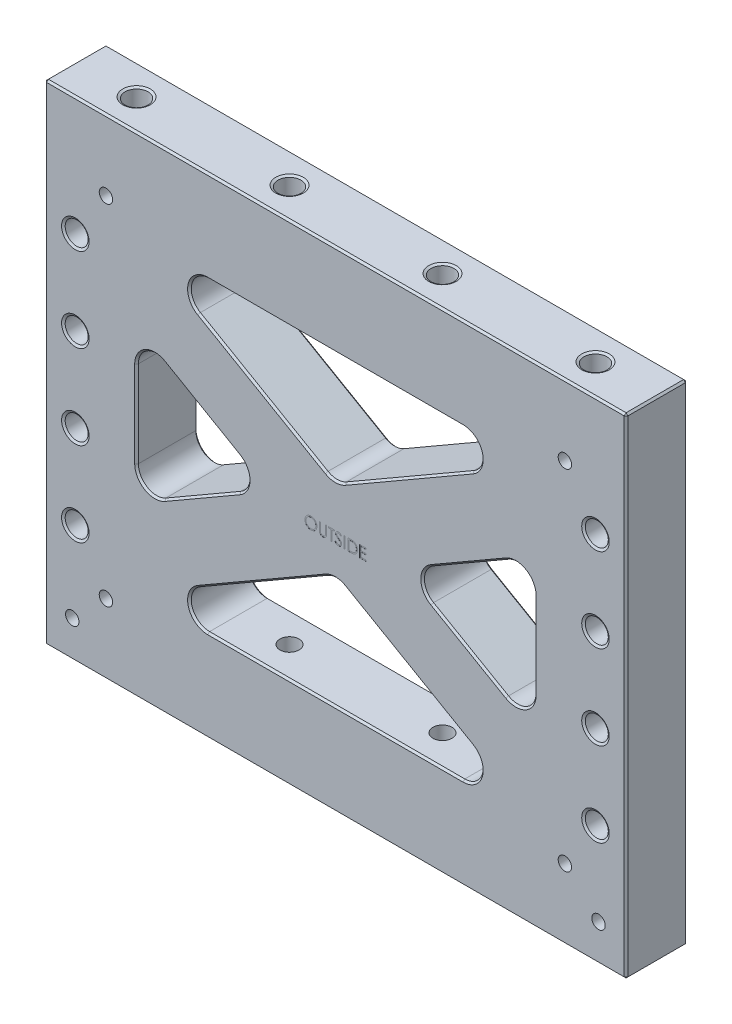
SolidWorks part; units mm, degrees
material "6061-T6 Al"
ref_plane "Front" through (0, 0, 0) normal (0, 0, 1) x (1, 0, 0)
ref_plane "Top" through (0, 0, 0) normal (0, 1, 0) x (1, 0, 0)
ref_plane "Right" through (0, 0, 0) normal (1, 0, 0) x (0, 0, -1)
sketch "Sketch1" plane through (0, 0, 0) normal (0, 0, 1) x (1, 0, 0)
  line L1 (-120.65, 0) -> (120.65, 0)
  line L2 (-120.65, 0) -> (-120.65, 203.2)
  line L3 (-120.65, 203.2) -> (120.65, 203.2)
  line L4 (120.65, 0) -> (120.65, 203.2)
  dimension "D1" = 241.3
  dimension "D2" = 203.2
extrude "Extrude1" add sketch "Sketch1" along normal blind 25.4
sketch "Sketch2" plane through (0, 0, 25.4) normal (0, 0, 1) x (1, 0, 0)
  line L0 (0, 165.1) -> (0, 203.2) construction
  line L1 (-82.55, 165.1) -> (82.55, 165.1)
  line L2 (-82.55, 165.1) -> (-82.55, 38.1)
  line L3 (-82.55, 38.1) -> (82.55, 38.1)
  line L4 (82.55, 165.1) -> (82.55, 38.1)
  line L5 (120.65, 203.2) -> (-120.65, 203.2) construction
  line L6 (0, 0) -> (0, 38.1) construction
  line L7 (120.65, 0) -> (120.65, 203.2) construction
  dimension "D1" = 38.1
  dimension "D2" = 38.1
extrude "Extrude2" cut sketch "Sketch2" against normal through all
sketch "Sketch3" plane through (0, 0, 25.4) normal (0, 0, 1) x (1, 0, 0)
  line L0 (81.4102, 38.1) -> (-138.5602, 165.1) construction
  line L1 (-82.55, 38.1) -> (82.55, 38.1) construction
  line L2 (-82.55, 149.2603) -> (82.55, 53.9397) construction
  line L3 (-82.55, 165.1) -> (-82.55, 38.1) construction
  line L4 (-82.55, 132.7625) -> (-82.55, 165.1)
  line L5 (-82.55, 165.1) -> (-81.4102, 165.1)
  line L6 (-81.4102, 165.1) -> (138.5602, 38.1) construction
  line L7 (-81.4102, 165.1) -> (82.55, 70.4375)
  line L8 (82.55, 38.1) -> (82.55, 165.1) construction
  line L9 (82.55, 70.4375) -> (82.55, 38.1)
  line L10 (82.55, 38.1) -> (81.4102, 38.1)
  line L11 (0, 101.6) -> (120.65, 101.6) construction
  line L12 (120.65, 0) -> (120.65, 203.2) construction
  line L13 (0, 101.6) -> (-7.1437, 89.2267) construction
  line L14 (0, 101.6) -> (7.1437, 113.9733) construction
  line L15 (82.55, 165.1) -> (-82.55, 165.1) construction
  line L16 (-81.4102, 165.1) -> (-138.5602, 165.1) construction
  line L17 (81.4102, 38.1) -> (-82.55, 132.7625)
  line L18 (81.4102, 38.1) -> (138.5602, 38.1) construction
  point P1 (0, 101.6)
  dimension "D1" = 30
  dimension "D2" = 28.575
extrude "Extrude3" add sketch "Sketch3" against normal up to surface (25.4 mm away) up to face at (0, 101.6, 0)
mirror "Mirror1" about plane through (0, 0, 0) normal (1, 0, 0) of "Extrude3"
fillet "Fillet1" radius 7.62 12 edges at (-81.4102, 38.1, 12.7) (81.4102, 38.1, 12.7) (0, 85.1022, 12.7) (81.4102, 165.1, 12.7) (-82.55, 132.7625, 12.7) (-82.55, 70.4375, 12.7) (-28.575, 101.6, 12.7) (82.55, 70.4375, 12.7) (82.55, 132.7625, 12.7) (28.575, 101.6, 12.7) (0, 118.0978, 12.7) (-81.4102, 165.1, 12.7)
chamfer "Chamfer1" distance 0.762 angle 45 48 edges at (30.296, 67.6108, 25.4) (30.296, 67.6108, 0) (60.3324, 43.7478, 0) (60.3324, 43.7478, 25.4) (0, 83.9234, 25.4) (0, 83.9234, 0) (0, 38.1, 0) (0, 38.1, 25.4) (-30.296, 67.6108, 25.4) (-60.3324, 43.7478, 0) (-60.3324, 43.7478, 25.4) (-30.296, 67.6108, 0) (82.55, 101.6, 0) (82.55, 101.6, 25.4) (78.74, 77.0366, 0) (78.74, 77.0366, 25.4) (78.74, 126.1634, 0) (78.74, 126.1634, 25.4) (55.5625, 86.0188, 25.4) (55.5625, 86.0188, 0) (55.5625, 117.1812, 25.4) (36.195, 101.6, 0) (36.195, 101.6, 25.4) (55.5625, 117.1812, 0) (30.296, 135.5892, 25.4) (0, 119.2766, 25.4) (0, 119.2766, 0) (60.3324, 159.4522, 0) (60.3324, 159.4522, 25.4) (-30.296, 135.5892, 25.4) (-30.296, 135.5892, 0) (0, 165.1, 0) (0, 165.1, 25.4) (-60.3324, 159.4522, 0) (-60.3324, 159.4522, 25.4) (30.296, 135.5892, 0) (-36.195, 101.6, 0) (-36.195, 101.6, 25.4) (-55.5625, 117.1812, 25.4) (-55.5625, 117.1812, 0) (-55.5625, 86.0188, 25.4) (-78.74, 126.1634, 0) (-78.74, 126.1634, 25.4) (-78.74, 77.0366, 0) (-78.74, 77.0366, 25.4) (-82.55, 101.6, 0) (-82.55, 101.6, 25.4) (-55.5625, 86.0188, 0)
chamfer "Chamfer2" distance 0.762 angle 45 12 edges at (0, 0, 0) (0, 0, 25.4) (-120.65, 101.6, 0) (-120.65, 101.6, 25.4) (-120.65, 0, 12.7) (0, 203.2, 0) (0, 203.2, 25.4) (-120.65, 203.2, 12.7) (120.65, 0, 12.7) (120.65, 101.6, 0) (120.65, 101.6, 25.4) (120.65, 203.2, 12.7)
hole_wizard "3/8-16 Tapped Hole1" positions "Sketch7" profile "Sketch6" tap size "3/8-16" standard "Ansi Inch"
sketch "Sketch7" plane through (0, 203.2, 0) normal (0, 1, 0) x (-1, 0, 0)
  line L1 (-95.25, 12.7) -> (-31.75, 12.7) construction
  line L2 (-31.75, 12.7) -> (31.75, 12.7) construction
  line L3 (31.75, 12.7) -> (95.25, 12.7) construction
  line L6 (120.65, 25.4) -> (120.65, 0) construction
  point P1 (31.75, 12.7)
  point P3 (-31.75, 12.7)
  point P25 (0, 12.7)
  point P29 (120.65, 12.7)
  dimension "D1" = 63.5
sketch "Sketch6" plane through (-31.75, 203.2, 12.7) normal (1, 0, 0) x (0, 0, 1)
  line L0 (0, 0) -> (0, 40.4847)
  line L1 (0, 40.4847) -> (3.9687, 38.1)
  line L2 (3.9687, 38.1) -> (3.9687, 25.4)
  line L3 (3.9687, 25.4) -> (4.7625, 25.4)
  line L5 (4.7625, 25.4) -> (4.7625, 0.5499)
  line L6 (4.7625, 0.5499) -> (5.715, 0)
  line L7 (5.715, 0) -> (0, 0)
  line L8 (-4.7625, 0.5499) -> (-5.715, 0) construction
  line L10 (0, 40.4847) -> (-3.9688, 38.1) construction
  line L11 (0, -6.35) -> (0, 107.95) construction
  dimension "Tap Drill Dia." = 7.9375
  dimension "Tap Drill Depth" = 38.1
  dimension "Thread Major Dia." = 9.525
  dimension "Thread Depth" = 25.4
  dimension "Near C'Sink Dia." = 11.43
  dimension "Near C'Sink Angle" = 120
  dimension "Drill Angle" = 118
hole_wizard "3/8-16 Tapped Hole2" positions "Sketch9" profile "Sketch8" tap size "3/8-16" standard "Ansi Inch"
sketch "Sketch9" plane through (0, 0, 0) normal (0, -1, 0) x (1, 0, 0)
  point P1 (-31.75, 12.7)
  point P4 (31.75, 12.7)
sketch "Sketch8" plane through (-31.75, 0, 12.7) normal (1, 0, 0) x (0, 0, -1)
  line L0 (0, 0) -> (0, 40.4847)
  line L1 (0, 40.4847) -> (3.9687, 38.1)
  line L2 (3.9687, 38.1) -> (3.9687, 25.4)
  line L3 (3.9687, 25.4) -> (4.7625, 25.4)
  line L5 (4.7625, 25.4) -> (4.7625, 0.5499)
  line L6 (4.7625, 0.5499) -> (5.715, 0)
  line L7 (5.715, 0) -> (0, 0)
  line L8 (-4.7625, 0.5499) -> (-5.715, 0) construction
  line L10 (0, 40.4847) -> (-3.9688, 38.1) construction
  line L11 (0, -6.35) -> (0, 107.95) construction
  dimension "Tap Drill Dia." = 7.9375
  dimension "Tap Drill Depth" = 38.1
  dimension "Thread Major Dia." = 9.525
  dimension "Thread Depth" = 25.4
  dimension "Near C'Sink Dia." = 11.43
  dimension "Near C'Sink Angle" = 120
  dimension "Drill Angle" = 118
hole_wizard "3/8-16 Tapped Hole3" positions "Sketch11" profile "Sketch10" tap size "3/8-16" standard "Ansi Inch"
sketch "Sketch11" plane through (0, 203.2, 0) normal (0, 1, 0) x (-1, 0, 0)
  line L0 (-95.25, 12.7) -> (-31.75, 12.7) construction
  line L1 (-31.75, 12.7) -> (31.75, 12.7) construction
  line L2 (31.75, 12.7) -> (95.25, 12.7) construction
  point P0 (95.25, 12.7)
  point P2 (-95.25, 12.7)
sketch "Sketch10" plane through (-95.25, 203.2, 12.7) normal (1, 0, 0) x (0, 0, 1)
  line L0 (0, 0) -> (0, 40.4847)
  line L1 (0, 40.4847) -> (3.9687, 38.1)
  line L2 (3.9687, 38.1) -> (3.9687, 25.4)
  line L3 (3.9687, 25.4) -> (4.7625, 25.4)
  line L5 (4.7625, 25.4) -> (4.7625, 0.5499)
  line L6 (4.7625, 0.5499) -> (5.715, 0)
  line L7 (5.715, 0) -> (0, 0)
  line L8 (-4.7625, 0.5499) -> (-5.715, 0) construction
  line L10 (0, 40.4847) -> (-3.9688, 38.1) construction
  line L11 (0, -6.35) -> (0, 107.95) construction
  dimension "Tap Drill Dia." = 7.9375
  dimension "Tap Drill Depth" = 38.1
  dimension "Thread Major Dia." = 9.525
  dimension "Thread Depth" = 25.4
  dimension "Near C'Sink Dia." = 11.43
  dimension "Near C'Sink Angle" = 120
  dimension "Drill Angle" = 118
hole_wizard "3/8-16 Tapped Hole4" positions "Sketch13" profile "Sketch12" tap size "3/8-16" standard "Ansi Inch"
sketch "Sketch13" plane through (0, 0, 0) normal (0, -1, 0) x (1, 0, 0)
  point P0 (-95.25, 12.7)
  point P1 (95.25, 12.7)
sketch "Sketch12" plane through (-95.25, 0, 12.7) normal (1, 0, 0) x (0, 0, -1)
  line L0 (0, 0) -> (0, 40.4847)
  line L1 (0, 40.4847) -> (3.9687, 38.1)
  line L2 (3.9687, 38.1) -> (3.9687, 25.4)
  line L3 (3.9687, 25.4) -> (4.7625, 25.4)
  line L5 (4.7625, 25.4) -> (4.7625, 0.5499)
  line L6 (4.7625, 0.5499) -> (5.715, 0)
  line L7 (5.715, 0) -> (0, 0)
  line L8 (-4.7625, 0.5499) -> (-5.715, 0) construction
  line L10 (0, 40.4847) -> (-3.9688, 38.1) construction
  line L11 (0, -6.35) -> (0, 107.95) construction
  dimension "Tap Drill Dia." = 7.9375
  dimension "Tap Drill Depth" = 38.1
  dimension "Thread Major Dia." = 9.525
  dimension "Thread Depth" = 25.4
  dimension "Near C'Sink Dia." = 11.43
  dimension "Near C'Sink Angle" = 120
  dimension "Drill Angle" = 118
hole_wizard "7/32 (0.21875) Vent Hole1" positions "Sketch5" profile "Sketch4" hole size "7/32" standard "Ansi Inch" end condition through all
sketch "Sketch5" plane through (0, 0, 25.4) normal (0, 0, 1) x (1, 0, 0)
  line L0 (-95.25, 173.99) -> (-31.75, 173.99) construction
  line L1 (-31.75, 173.99) -> (31.75, 173.99) construction
  line L2 (31.75, 173.99) -> (95.25, 173.99) construction
  line L5 (0, -13.97) -> (0, 13.97) construction
  line L6 (120.65, 203.2) -> (-120.65, 203.2) construction
  line L7 (-95.25, 173.99) -> (-95.25, 203.2) construction
  line L10 (-95.25, 29.21) -> (-95.25, 0) construction
  line L11 (-120.65, 0) -> (120.65, 0) construction
  line L13 (-119.888, 203.2) -> (119.888, 203.2) construction
  point P0 (-95.25, 173.99)
  point P5 (95.25, 173.99)
  point P7 (-95.25, 29.21)
  point P13 (95.25, 29.21)
  point P26 (0, 173.99)
  dimension "D1" = 63.5
  dimension "D2" = 29.21
sketch "Sketch4" plane through (-95.25, 173.99, 25.4) normal (1, 0, 0) x (0, -1, 0)
  line L0 (0, 0) -> (0, 25.4)
  line L1 (0, 25.4) -> (2.7781, 25.4)
  line L2 (2.7781, 25.4) -> (2.7781, 0)
  line L5 (2.7781, 0) -> (0, 0)
  line L11 (0, -6.35) -> (0, 107.95) construction
  dimension "Thru Hole Dia." = 5.5562
  dimension "Thru Hole Depth" = 25.4
hole_wizard "3/8-16 Tapped Hole5" positions "Sketch15" profile "Sketch14" tap size "3/8-16" standard "Ansi Inch" end condition through all
sketch "Sketch15" plane through (8.7974, 80.9292, 0) normal (0, 0, 1) x (1, 0, 0)
  line L0 (99.1526, 73.0583) -> (111.8526, 73.0583) construction
  line L1 (111.8526, 121.5088) -> (111.8526, -80.1672) construction
  line L6 (-116.7474, 73.0583) -> (-116.7474, 38.1333) construction
  line L7 (-116.7474, 38.1333) -> (-116.7474, 3.2083) construction
  line L8 (-116.7474, 3.2083) -> (-116.7474, -31.7167) construction
  line L11 (-116.7474, 20.6708) -> (-129.4474, 20.6708) construction
  line L12 (-129.4474, -80.1672) -> (-129.4474, 121.5088) construction
  point P0 (-116.7474, 73.0583)
  point P1 (-116.7474, 38.1333)
  point P3 (-116.7474, 3.2083)
  point P5 (-116.7474, -31.7167)
  point P7 (99.1526, 73.0583)
  point P9 (99.1526, 38.1333)
  point P11 (99.1526, 3.2083)
  point P13 (99.1526, -31.7167)
  dimension "D1" = 12.7
  dimension "D2" = 34.925
sketch "Sketch14" plane through (-107.95, 153.9875, 0) normal (1, 0, 0) x (0, 1, 0)
  line L0 (0, 0) -> (0, 25.4)
  line L1 (0, 25.4) -> (5.715, 25.4)
  line L2 (4.7625, 24.8501) -> (4.7625, 0.5499)
  line L3 (4.7625, 0.5499) -> (5.715, 0)
  line L5 (5.715, 0) -> (0, 0)
  line L6 (-4.7625, 0.5499) -> (-5.715, 0) construction
  line L7 (5.715, 25.4) -> (4.7625, 24.8501)
  line L8 (-5.715, 25.4) -> (-4.7625, 24.8501) construction
  line L11 (0, -6.35) -> (0, 107.95) construction
  dimension "Thread Major Dia." = 9.525
  dimension "Thru Tap Drill Depth" = 25.4
  dimension "Near C'Sink Dia." = 11.43
  dimension "Near C'Sink Angle" = 120
  dimension "Far C'Sink Dia." = 11.43
  dimension "Far C'Sink Angle" = 120
sketch "Sketch16" [suppressed] plane through (0, 0, 0) normal (0, -1, 0) x (1, 0, 0)
  line L4 (-120.65, 0) -> (120.65, 0)
  line L5 (120.65, 0) -> (120.65, 25.4)
  line L6 (120.65, 25.4) -> (-120.65, 25.4)
  line L7 (-120.65, 25.4) -> (-120.65, 0)
  line L8 (-120.65, 0) -> (120.65, 0)
  line L9 (120.65, 0) -> (120.65, 25.4)
  line L10 (120.65, 25.4) -> (-120.65, 25.4)
  line L11 (-120.65, 25.4) -> (-120.65, 0)
  dimension "D1" = 0
extrude "Extrude4" [suppressed] cut sketch "Sketch16" against normal blind 0.0254
sketch "Sketch17" [suppressed] plane through (0, 0.0254, 0) normal (0, -1, 0) x (1, 0, 0)
  line L0 (120.65, 25.4) -> (-120.65, 25.4) construction
  line L1 (-44.45, 25.4) -> (-19.05, 25.4)
  line L2 (-44.45, 25.4) -> (-44.45, 0)
  line L3 (-44.45, 0) -> (-19.05, 0)
  line L4 (-19.05, 25.4) -> (-19.05, 0)
  line L5 (-120.65, 0) -> (120.65, 0) construction
  line L6 (-19.05, 12.7) -> (19.05, 12.7) construction
  line L7 (-107.95, 25.4) -> (-82.55, 25.4)
  line L8 (-107.95, 25.4) -> (-107.95, 0)
  line L9 (-107.95, 0) -> (-82.55, 0)
  line L10 (-82.55, 25.4) -> (-82.55, 0)
  line L11 (19.05, 25.4) -> (44.45, 25.4)
  line L12 (19.05, 25.4) -> (19.05, 0)
  line L13 (19.05, 0) -> (44.45, 0)
  line L14 (44.45, 25.4) -> (44.45, 0)
  line L15 (82.55, 25.4) -> (107.95, 25.4)
  line L16 (82.55, 25.4) -> (82.55, 0)
  line L17 (82.55, 0) -> (107.95, 0)
  line L18 (107.95, 25.4) -> (107.95, 0)
  line L19 (44.45, 12.7) -> (82.55, 12.7) construction
  line L20 (-82.55, 12.7) -> (-44.45, 12.7) construction
  point P26 (0, 12.7)
  dimension "D1" = 25.4
  dimension "D2" = 38.1
extrude "Extrude5" [suppressed] add sketch "Sketch17" along normal blind 0.0254
sketch "Sketch19" [suppressed] plane through (0, 184.15, 0) normal (0, 1, 0) x (1, 0, 0)
  line L4 (120.65, 0) -> (-120.65, 0)
  line L5 (-120.65, 0) -> (-120.65, -25.4)
  line L6 (-120.65, -25.4) -> (120.65, -25.4)
  line L7 (120.65, -25.4) -> (120.65, 0)
  line L8 (120.65, 0) -> (-120.65, 0)
  line L9 (-120.65, 0) -> (-120.65, -25.4)
  line L10 (-120.65, -25.4) -> (120.65, -25.4)
  line L11 (120.65, -25.4) -> (120.65, 0)
  dimension "D1" = 0
extrude "Extrude7" [suppressed] cut sketch "Sketch19" against normal blind 0.0254
sketch "Sketch18" [suppressed] plane through (0, 184.1246, 0) normal (0, 1, 0) x (1, 0, 0)
  line L1 (-44.45, 0) -> (-19.05, 0)
  line L2 (-44.45, 0) -> (-44.45, -25.4)
  line L3 (-44.45, -25.4) -> (-19.05, -25.4)
  line L4 (-19.05, 0) -> (-19.05, -25.4)
  line L6 (-82.55, -12.7) -> (-44.45, -12.7) construction
  line L7 (-107.95, 0) -> (-82.55, 0)
  line L8 (-107.95, 0) -> (-107.95, -25.4)
  line L9 (-107.95, -25.4) -> (-82.55, -25.4)
  line L10 (-82.55, 0) -> (-82.55, -25.4)
  line L11 (19.05, 0) -> (44.45, 0)
  line L12 (19.05, 0) -> (19.05, -25.4)
  line L13 (19.05, -25.4) -> (44.45, -25.4)
  line L14 (44.45, 0) -> (44.45, -25.4)
  line L15 (82.55, 0) -> (107.95, 0)
  line L16 (82.55, 0) -> (82.55, -25.4)
  line L17 (82.55, -25.4) -> (107.95, -25.4)
  line L18 (107.95, 0) -> (107.95, -25.4)
  line L19 (-19.05, -12.7) -> (19.05, -12.7) construction
  line L20 (44.45, -12.7) -> (82.55, -12.7) construction
  line L21 (120.65, 0) -> (-120.65, 0) construction
  line L22 (-120.65, -25.4) -> (120.65, -25.4) construction
  point P26 (0, -12.7)
  dimension "D1" = 38.1
  dimension "D2" = 25.4
extrude "Extrude6" [suppressed] add sketch "Sketch18" along normal blind 0.0254
sketch "Sketch20" [suppressed] plane through (0, 184.15, 0) normal (0, 1, 0) x (1, 0, 0)
  line L0 (107.95, -25.4) -> (107.95, 0) construction
  line L1 (-107.95, 0) -> (107.95, 0)
  line L2 (-107.95, 0) -> (-107.95, -3.81)
  line L3 (-107.95, -3.81) -> (107.95, -3.81)
  line L4 (107.95, 0) -> (107.95, -3.81)
  line L5 (107.95, -25.4) -> (120.65, -25.4) construction
  line L6 (107.95, -25.4) -> (-107.95, -25.4)
  line L7 (107.95, -25.4) -> (107.95, -21.59)
  line L8 (107.95, -21.59) -> (-107.95, -21.59)
  line L9 (-107.95, -25.4) -> (-107.95, -21.59)
  line L10 (-107.95, 0) -> (-107.95, -25.4) construction
  dimension "D1" = 3.81
extrude "Extrude8" [suppressed] cut sketch "Sketch20" against normal up to surface (0.0254 mm away)
sketch "Sketch21" [suppressed] plane through (0, 0, 0) normal (0, -1, 0) x (1, 0, 0)
  line L0 (107.95, 0) -> (107.95, 25.4) construction
  line L1 (-107.95, 25.4) -> (107.95, 25.4)
  line L2 (-107.95, 25.4) -> (-107.95, 21.59)
  line L3 (-107.95, 21.59) -> (107.95, 21.59)
  line L4 (107.95, 25.4) -> (107.95, 21.59)
  line L6 (-107.95, 0) -> (107.95, 0)
  line L7 (-107.95, 0) -> (-107.95, 3.81)
  line L8 (-107.95, 3.81) -> (107.95, 3.81)
  line L9 (107.95, 0) -> (107.95, 3.81)
  dimension "D1" = 3.81
extrude "Extrude9" [suppressed] cut sketch "Sketch21" against normal up to surface (0.0254 mm away)
sketch "Sketch22" [suppressed] plane through (0, 0, 25.4) normal (0, 0, 1) x (1, 0, 0)
  line L0 (-82.55, 125.0706) -> (-82.55, 59.0794)
  line L1 (-82.55, 59.0794) -> (-25.4, 92.075)
  line L2 (-25.4, 92.075) -> (-82.55, 125.0706)
  line L3 (0, 0) -> (0, 139.6976) construction
  line L4 (33.02, 92.075) -> (104.387, 92.075) construction
  line L5 (-71.12, 65.6785) -> (-36.83, 85.4759) construction
  line L6 (-82.55, 111.8723) -> (-82.55, 72.2777) construction
  line L7 (-71.12, 118.4715) -> (-36.83, 98.6741) construction
  line L8 (25.4, 92.075) -> (82.55, 125.0706)
  line L9 (82.55, 59.0794) -> (25.4, 92.075)
  line L10 (82.55, 125.0706) -> (82.55, 59.0794)
  line L11 (-68.0874, 146.05) -> (0, 106.7397)
  line L12 (0, 106.7397) -> (68.0874, 146.05)
  line L13 (68.0874, 146.05) -> (-68.0874, 146.05)
  line L14 (39.6492, 146.05) -> (-39.6492, 146.05) construction
  line L15 (3.81, 108.9394) -> (43.4592, 131.8309) construction
  line L16 (-3.81, 108.9394) -> (-43.4592, 131.8309) construction
  line L17 (0, 77.4103) -> (68.0874, 38.1)
  line L18 (68.0874, 38.1) -> (-68.0874, 38.1)
  line L19 (-68.0874, 38.1) -> (0, 77.4103)
  arc A0 (36.83, 98.6741) -> (36.83, 85.4759) centre (40.64, 92.075) ccw construction
extrude "Extrude10" [suppressed] cut sketch "Sketch22" against normal through all
hole_wizard "3/8 (0.375) Diameter Hole2" positions "Sketch32" profile "Sketch31" hole size "3/8" standard "Ansi Inch"
sketch "Sketch32" plane through (0, 0, 0) normal (0, -1, 0) x (1, 0, 0)
  line L0 (-109.22, 12.7) -> (109.22, 12.7) construction
  line L3 (-120.65, 0.762) -> (-120.65, 24.638) construction
  point P0 (-109.22, 12.7)
  point P7 (0, 12.7)
  point P11 (-120.65, 12.7)
  dimension "D1" = 13.97
sketch "Sketch31" plane through (-109.22, 0, 12.7) normal (1, 0, 0) x (0, 0, -1)
  line L0 (0, 0) -> (0, 21.9169)
  line L1 (0, 21.9169) -> (4.7714, 19.05)
  line L2 (4.7714, 19.05) -> (4.7714, 2.3406)
  line L3 (4.7714, 2.3406) -> (7.112, 0)
  line L5 (7.112, 0) -> (0, 0)
  line L6 (-4.7714, 2.3406) -> (-7.112, 0) construction
  line L10 (0, 21.9169) -> (-4.7714, 19.05) construction
  line L11 (0, -6.35) -> (0, 107.95) construction
  dimension "Hole Dia." = 9.5428
  dimension "Hole Depth" = 19.05
  dimension "Near C'Sink Dia." = 14.224
  dimension "Near C'Sink Angle" = 90
  dimension "Drill Angle" = 118
sketch "Sketch33" plane through (0, 0, 0) normal (0, -1, 0) x (1, 0, 0)
  line L0 (108.458, 12.7) -> (109.982, 12.7) construction
  line L1 (108.458, 17.4714) -> (109.982, 17.4714)
  line L2 (108.458, 7.9286) -> (109.982, 7.9286)
  arc A0 (108.458, 17.4714) -> (108.458, 7.9286) centre (108.458, 12.7) ccw
  arc A1 (109.982, 7.9286) -> (109.982, 17.4714) centre (109.982, 12.7) ccw
  circle A2 centre (-109.22, 12.7) radius 4.7714 construction
  point P2 (109.22, 12.7)
  dimension "D1" = 1.524
extrude "Extrude14" cut sketch "Sketch33" against normal blind 19.05
chamfer "Chamfer4" distance 2.286 angle 45 4 edges at (114.7534, 0, 12.7) (109.22, 0, 17.4714) (109.22, 0, 7.9286) (103.6866, 0, 12.7)
hole_wizard "7/32 (0.21875) Diameter Hole3" positions "Sketch35" profile "Sketch34" hole size "7/32" standard "Ansi Inch" end condition through all
sketch "Sketch35" plane through (0, 0, 25.4) normal (0, 0, 1) x (1, 0, 0)
  line L1 (-109.22, 15.24) -> (109.22, 15.24) construction
  line L2 (119.888, 0) -> (-119.888, 0) construction
  line L4 (-120.65, 0.762) -> (-120.65, 202.438) construction
  line L5 (120.65, 202.438) -> (120.65, 0.762) construction
  point P0 (-109.22, 15.24)
  point P1 (109.22, 15.24)
  dimension "D1" = 15.24
  dimension "D2" = 11.43
  dimension "D3" = 11.43
sketch "Sketch34" plane through (-109.22, 15.24, 25.4) normal (1, 0, 0) x (0, -1, 0)
  line L0 (0, 0) -> (0, 25.4)
  line L1 (0, 25.4) -> (2.7781, 25.4)
  line L2 (2.7781, 25.4) -> (2.7781, 0)
  line L5 (2.7781, 0) -> (0, 0)
  line L11 (0, -6.35) -> (0, 107.95) construction
  dimension "Thru Hole Dia." = 5.5562
  dimension "Thru Hole Depth" = 25.4
sketch "Sketch36" plane through (0, 0, 25.4) normal (0, 0, 1) x (1, 0, 0)
  line L0 (-20.833, 96.532) -> (20.833, 96.532) construction
  line L1 (0, 84.6854) -> (0, 96.532) construction
  arc A0 (4.191, 83.5624) -> (-4.191, 83.5624) centre (0, 76.3034) ccw construction
  text T0 "OUTSIDE" font "Century Gothic" height in points 18
extrude "Extrude15" cut sketch "Sketch36" against normal blind 0.0254
